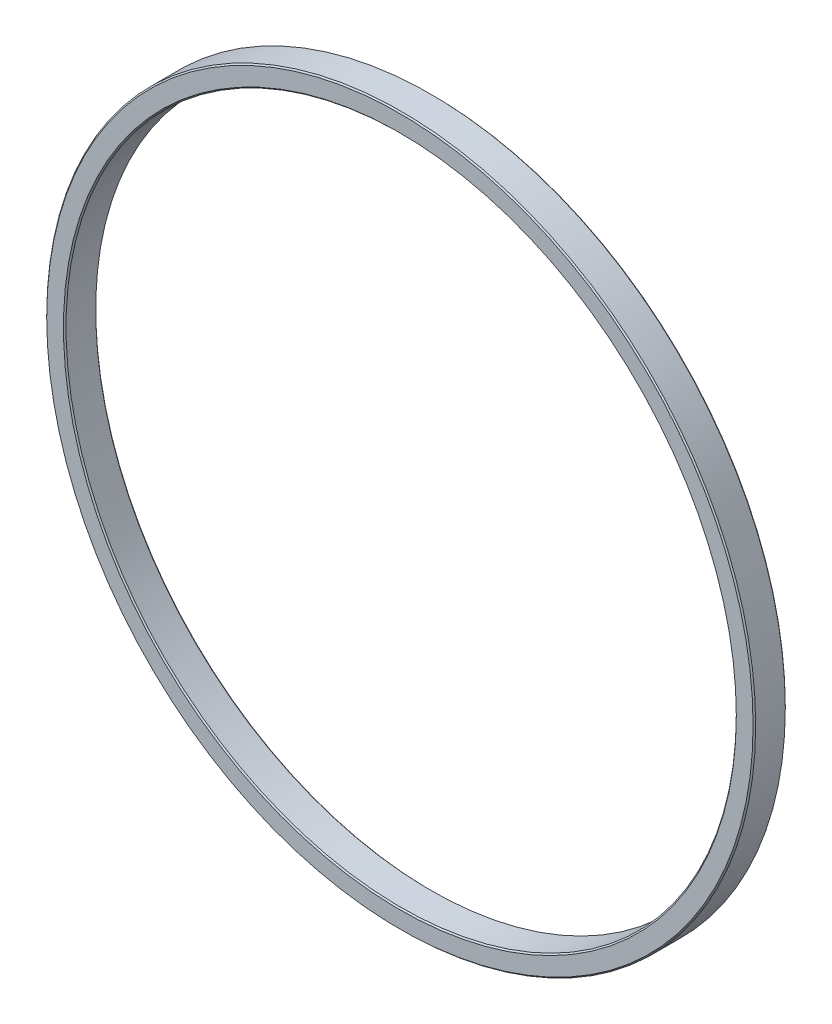
SolidWorks part; units mm, degrees
material "1.0114 (S235J0)"
ref_plane "Piano frontale" through (0, 0, 0) normal (0, 0, 1) x (1, 0, 0)
ref_plane "Piano superiore" through (0, 0, 0) normal (0, 1, 0) x (1, 0, 0)
ref_plane "Piano destro" through (0, 0, 0) normal (1, 0, 0) x (0, 0, -1)
sketch "Schizzo1" plane through (0, 0, 0) normal (0, 0, 1) x (1, 0, 0)
  circle A0 centre (0, 0) radius 52
  circle A1 centre (0, 0) radius 55
  dimension "D1" = 110
  dimension "D2" = 104
extrude "Estrusione-Estrusione1" add sketch "Schizzo1" along normal blind 5
chamfer "Smusso1" distance 0.2 angle 45 4 edges at (52, 0, 5) (55, 0, 5) (52, 0, 0) (55, 0, 0)
